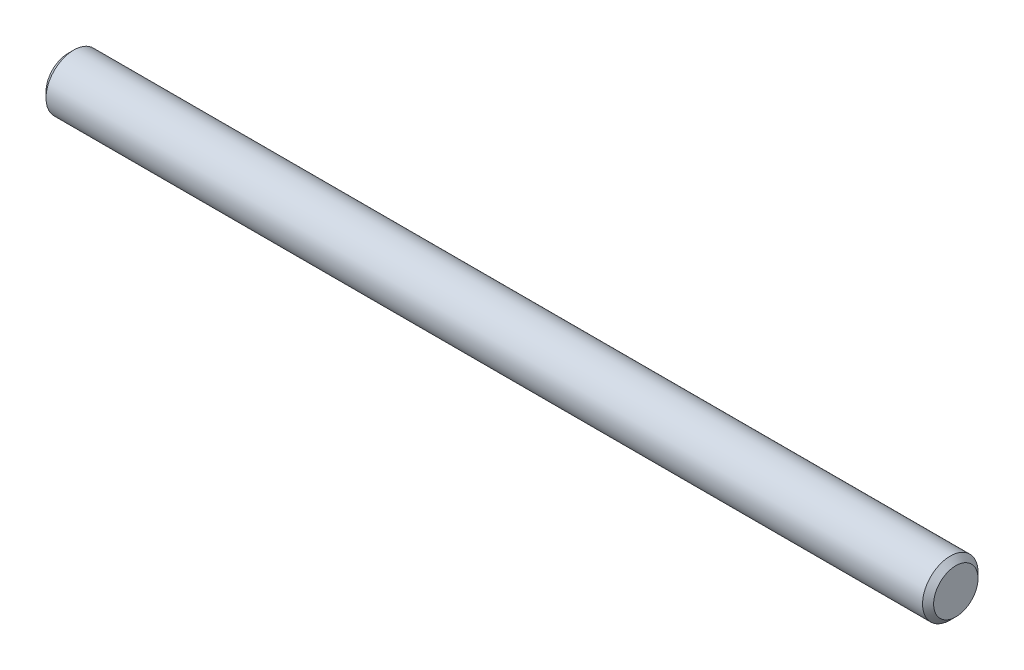
SolidWorks part; units mm, degrees
ref_plane "Front" through (0, 0, 0) normal (0, 0, 1) x (1, 0, 0)
ref_plane "Top" through (0, 0, 0) normal (0, 1, 0) x (1, 0, 0)
ref_plane "Right" through (0, 0, 0) normal (1, 0, 0) x (0, 0, -1)
sketch "Sketch1" plane through (0, 0, 0) normal (0, 0, 1) x (1, 0, 0)
  line L0 (-25.4, 0) -> (25.4, 0) construction
  line L1 (25.4, 1.5875) -> (25.4, -1.5875) construction
  line L2 (-25.4, 1.5875) -> (-25.4, -1.5875) construction
  dimension "Length" = 50.8
  dimension "Diameter" = 3.175
sketch "Sketch2" plane through (0, 0, 0) normal (1, 0, 0) x (0, 0, -1)
  circle A0 centre (0, 0) radius 1.5875
extrude "Extrude1" add sketch "Sketch2" against normal up to vertex (25.4 mm away) and the other way up to vertex (25.4 mm away) up to point (-25.4, 1.5875, 0) other way up to point (25.4, 1.5875, 0)
chamfer "Chamfer1" distance 0.3175 angle 45 2 edges at (25.4, 0, -1.5875) (-25.4, 0, -1.5875)
equation "\"D1@Chamfer1\" = \"Diameter@Sketch1\"*.1"
